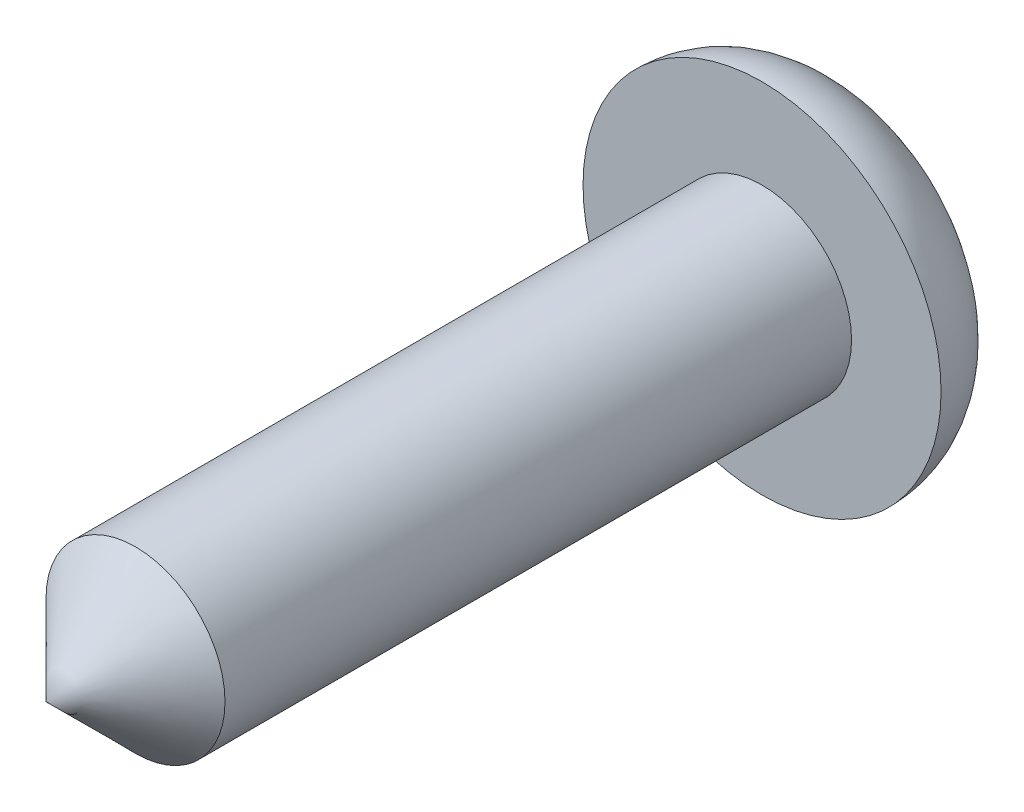
SolidWorks part; units mm, degrees
material "1023 Carbon Steel Sheet (SS)"
ref_plane "Front Plane" through (0, 0, 0) normal (0, 0, 1) x (1, 0, 0)
ref_plane "Top Plane" through (0, 0, 0) normal (0, 1, 0) x (1, 0, 0)
ref_plane "Right Plane" through (0, 0, 0) normal (1, 0, 0) x (0, 0, -1)
sketch "Sketch1" plane through (0, 0, 0) normal (0, 1, 0) x (1, 0, 0)
  line L0 (-1, -1) -> (-1, -8)
  line L1 (-1, -8) -> (0, -9)
  line L2 (0, -9) -> (0, 0) construction
  line L3 (0, 0) -> (-1, 0)
  line L4 (-2, -1) -> (-1, -1)
  line L5 (0, 0) -> (0, -9)
  arc A0 (-1, 0) -> (-2, -1) centre (-1, -1) ccw
  dimension "D1" = 1
  dimension "D2" = 2
  dimension "D3" = 8
  dimension "D4" = 45
revolve "Revolve1" add sketch "Sketch1" angle 360 about L2
